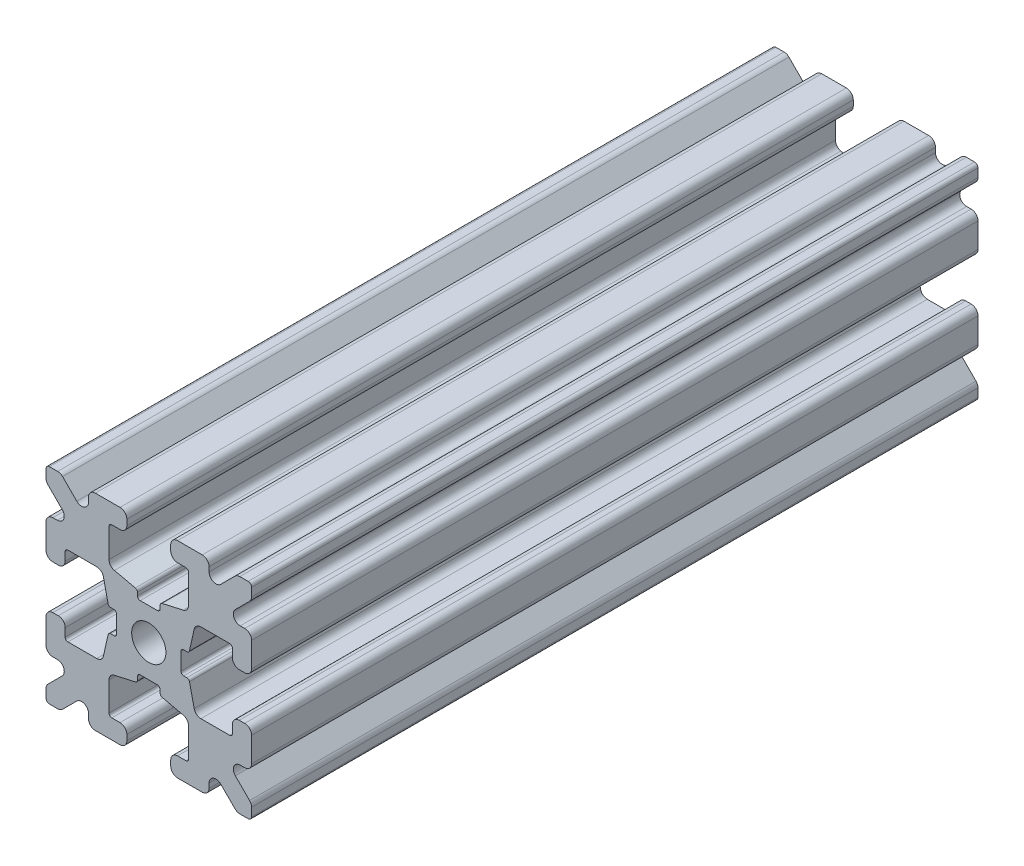
SolidWorks part; units mm, degrees
ref_plane "Front Plane" through (0, 0, 0) normal (0, 0, 1) x (1, 0, 0)
ref_plane "Top Plane" through (0, 0, 0) normal (0, 1, 0) x (1, 0, 0)
ref_plane "Right Plane" through (0, 0, 0) normal (1, 0, 0) x (0, 0, -1)
sketch "Sketch1" plane through (0, 0, 0) normal (0, 0, 1) x (1, 0, 0)
  line L1 (-7.5, -7.5) -> (7.5, -7.5)
  line L2 (-7.5, -7.5) -> (-7.5, 7.5)
  line L3 (-7.5, 7.5) -> (7.5, 7.5)
  line L4 (7.5, -7.5) -> (7.5, 7.5)
  line L5 (-7.5, -7.5) -> (7.5, 7.5) construction
  line L6 (-7.5, 7.5) -> (7.5, -7.5) construction
  circle A0 centre (0, 0) radius 1.25
  point P0 (0, 0)
  dimension "D2" = 2.5
  dimension "D1" = 15
extrude "Boss-Extrude1" add sketch "Sketch1" along normal mid plane 53
fillet "Fillet1" radius 0.25 4 edges at (7.5, -7.5, 0) (-7.5, -7.5, 0) (7.5, 7.5, 0) (-7.5, 7.5, 0)
sketch "Sketch2" plane through (0, 0, 26.5) normal (0, 0, 1) x (1, 0, 0)
  line L0 (-7.5, 7.25) -> (-7.5, -7.25) construction
  line L1 (-7.5, 1.6) -> (-6.1, 1.6)
  line L2 (-7.5, 1.6) -> (-7.5, -1.6)
  line L3 (-7.5, -1.6) -> (-6.1, -1.6)
  line L4 (-6.1, 1.6) -> (-6.1, 2.9)
  line L5 (0, 0) -> (-12.1036, 0) construction
  line L6 (-6.1, -2.9) -> (-3.4, -2.9)
  line L7 (0, 0) -> (-7.25, 7.25) construction
  line L8 (-6.1, 2.9) -> (-3.4, 2.9)
  line L9 (-3.4, -2.9) -> (-3.4, 2.9)
  line L10 (55, 0) -> (-55, 0) construction
  line L11 (-6.1, -2.9) -> (-6.1, -1.6)
  line L12 (2.9, 6.1) -> (1.6, 6.1)
  line L13 (2.9, 3.4) -> (-2.9, 3.4)
  line L14 (-2.9, 6.1) -> (-2.9, 3.4)
  line L15 (2.9, 6.1) -> (2.9, 3.4)
  line L16 (-1.6, 6.1) -> (-2.9, 6.1)
  line L17 (1.6, 7.5) -> (1.6, 6.1)
  line L18 (-1.6, 7.5) -> (1.6, 7.5)
  line L19 (-1.6, 7.5) -> (-1.6, 6.1)
  line L20 (-1.6, -7.5) -> (-1.6, -6.1)
  line L21 (-1.6, -7.5) -> (1.6, -7.5)
  line L22 (1.6, -7.5) -> (1.6, -6.1)
  line L23 (-1.6, -6.1) -> (-2.9, -6.1)
  line L24 (2.9, -6.1) -> (2.9, -3.4)
  line L25 (-2.9, -6.1) -> (-2.9, -3.4)
  line L26 (2.9, -3.4) -> (-2.9, -3.4)
  line L27 (2.9, -6.1) -> (1.6, -6.1)
  line L28 (6.1, -2.9) -> (6.1, -1.6)
  line L29 (3.4, -2.9) -> (3.4, 2.9)
  line L30 (6.1, 2.9) -> (3.4, 2.9)
  line L31 (6.1, -2.9) -> (3.4, -2.9)
  line L32 (6.1, 1.6) -> (6.1, 2.9)
  line L33 (7.5, -1.6) -> (6.1, -1.6)
  line L34 (7.5, 1.6) -> (7.5, -1.6)
  line L35 (7.5, 1.6) -> (6.1, 1.6)
  dimension "D1" = 3.2
  dimension "D2" = 5.8
  dimension "D3" = 1.4
  dimension "D4" = 2.7
extrude "Cut-Extrude1" cut sketch "Sketch2" against normal through all
sketch "Sketch4" plane through (0, 0, 26.5) normal (0, 0, 1) x (1, 0, 0)
  line L0 (-3.4, 2.9) -> (-2.75, 0)
  line L1 (55, 0) -> (-55, 0) construction
  line L2 (-2.75, 0) -> (-3.4, -2.9)
  line L3 (-3.4, -2.9) -> (-3.4, 2.9) construction
  line L4 (-3.4, 2.9) -> (-3.4, -2.9)
  line L5 (-2.9, 3.4) -> (0, 2.75)
  line L6 (0, 2.75) -> (2.9, 3.4)
  line L7 (2.9, 3.4) -> (-2.9, 3.4)
  line L8 (3.4, 2.9) -> (2.75, 0)
  line L9 (2.75, 0) -> (3.4, -2.9)
  line L10 (3.4, -2.9) -> (3.4, 2.9)
  line L11 (-2.9, -3.4) -> (0, -2.75)
  line L12 (0, -2.75) -> (2.9, -3.4)
  line L13 (2.9, -3.4) -> (-2.9, -3.4)
  circle A2 centre (0, 0) radius 2.75
  circle A3 centre (0, 0) radius 2.75 construction
  dimension "D1" = 1.5
extrude "Cut-Extrude3" cut sketch "Sketch4" against normal through all
fillet "Fillet3" radius 0.5 16 edges at (-6.1, -1.6, 0) (-7.5, -1.6, 0) (-6.1, 1.6, 0) (-7.5, 1.6, 0) (-1.6, -7.5, 0) (-1.6, -6.1, 0) (1.6, -7.5, 0) (1.6, -6.1, 0) (6.1, -1.6, 0) (7.5, -1.6, 0) (7.5, 1.6, 0) (6.1, 1.6, 0) (1.6, 7.5, 0) (1.6, 6.1, 0) (-1.6, 7.5, 0) (-1.6, 6.1, 0)
fillet "Fillet4" radius 0.5 8 edges at (-3.4, 2.9, 0) (-3.4, -2.9, 0) (2.9, -3.4, 0) (-2.9, -3.4, 0) (3.4, -2.9, 0) (3.4, 2.9, 0) (-2.9, 3.4, 0) (2.9, 3.4, 0)
fillet "Fillet5" radius 3 4 edges at (0, -2.75, 0) (2.75, 0, 0) (-2.75, 0, 0) (0, 2.75, 0)
fillet "Fillet6" radius 0.2 8 edges at (-2.9, -6.1, 0) (2.9, -6.1, 0) (6.1, -2.9, 0) (6.1, 2.9, 0) (2.9, 6.1, 0) (-2.9, 6.1, 0) (-6.1, -2.9, 0) (-6.1, 2.9, 0)
sketch "Sketch5" plane through (0, 0, 26.5) normal (0, 0, 1) x (1, 0, 0)
  line L0 (0, 0) -> (-7.25, 7.25) construction
  line L1 (-7.5, 6.4393) -> (-5.4607, 4.4)
  line L2 (-6.4393, 7.5) -> (-4.4, 5.4607)
  line L3 (-7.5, 4.4) -> (-5.4607, 4.4)
  line L4 (-3.8003, 2.9) -> (-5.9, 2.9) construction
  line L5 (0, 0) -> (-12.1819, 0) construction
  line L6 (-4.4, 7.5) -> (-4.4, 5.4607)
  line L7 (-2.9, 5.9) -> (-2.9, 3.8003) construction
  line L8 (-7.5, 6.4393) -> (-7.5, 4.4)
  line L9 (-7.5, 7.25) -> (-7.5, 2.1) construction
  line L10 (2.1, -7.5) -> (7.25, -7.5) construction
  line L11 (7.5, -7.25) -> (7.5, -2.1) construction
  line L12 (7.25, 7.5) -> (2.1, 7.5) construction
  line L13 (-2.1, 7.5) -> (-7.25, 7.5) construction
  line L14 (-4.4, 7.5) -> (-6.4393, 7.5)
  line L16 (55, 0) -> (-55, 0) construction
  line L17 (0, 0) -> (0, 10.993) construction
  line L18 (0, -54.6431) -> (0, 54.6431) construction
  line L20 (4.4, 7.5) -> (6.4393, 7.5)
  line L22 (7.5, 6.4393) -> (7.5, 4.4)
  line L23 (4.4, 7.5) -> (4.4, 5.4607)
  line L24 (7.5, 4.4) -> (5.4607, 4.4)
  line L25 (6.4393, 7.5) -> (4.4, 5.4607)
  line L26 (7.5, 6.4393) -> (5.4607, 4.4)
  line L27 (7.5, -6.4393) -> (5.4607, -4.4)
  line L28 (6.4393, -7.5) -> (4.4, -5.4607)
  line L29 (7.5, -4.4) -> (5.4607, -4.4)
  line L30 (4.4, -7.5) -> (4.4, -5.4607)
  line L31 (7.5, -6.4393) -> (7.5, -4.4)
  line L33 (4.4, -7.5) -> (6.4393, -7.5)
  line L36 (-4.4, -7.5) -> (-6.4393, -7.5)
  line L38 (-7.5, -6.4393) -> (-7.5, -4.4)
  line L39 (-4.4, -7.5) -> (-4.4, -5.4607)
  line L40 (-7.5, -4.4) -> (-5.4607, -4.4)
  line L41 (-6.4393, -7.5) -> (-4.4, -5.4607)
  line L42 (-7.5, -6.4393) -> (-5.4607, -4.4)
  dimension "D1" = 1.5
  dimension "D2" = 1.5
  dimension "D3" = 1.5
extrude "Cut-Extrude4" cut sketch "Sketch5" against normal through all
fillet "Fillet8" radius 0.5 24 edges at (-5.4607, 4.4, 0) (-7.5, 4.4, 0) (-5.4607, -4.4, 0) (-7.5, -4.4, 0) (-4.4, -7.5, 0) (-4.4, -5.4607, 0) (4.4, -7.5, 0) (4.4, -5.4607, 0) (5.4607, -4.4, 0) (7.5, -4.4, 0) (7.5, 4.4, 0) (5.4607, 4.4, 0) (4.4, 5.4607, 0) (4.4, 7.5, 0) (-4.4, 5.4607, 0) (-4.4, 7.5, 0) (-6.4393, 7.5, 0) (-7.5, 6.4393, 0) (6.4393, 7.5, 0) (7.5, 6.4393, 0) (6.4393, -7.5, 0) (7.5, -6.4393, 0) (-6.4393, -7.5, 0) (-7.5, -6.4393, 0)
sketch "Sketch6" plane through (0, 0, 26.5) normal (0, 0, 1) x (1, 0, 0)
  line L0 (0, 0) -> (0, 11.013) construction
  line L1 (0.6561, 2.8971) -> (2.1235, 2.8971) construction
  line L2 (0, -54.6431) -> (0, 54.6431) construction
  line L3 (0, 0) -> (7.25, 7.25) construction
  line L4 (7.5, 0.8255) -> (7.5, -0.8255)
  line L5 (2.3471, 0.8255) -> (7.5, 0.8255)
  line L6 (0, 0) -> (12.4016, 0) construction
  line L7 (0.8255, -7.5) -> (-0.8255, -7.5)
  line L8 (2.3471, -0.8255) -> (2.3471, 0.8255)
  line L9 (0.8255, -2.3471) -> (0.8255, -7.5)
  line L10 (7.5, -0.8255) -> (2.3471, -0.8255)
  line L11 (-7.5, -0.8255) -> (-2.3471, -0.8255)
  line L12 (-2.3471, -0.8255) -> (-2.3471, 0.8255)
  line L13 (-0.8255, -2.3471) -> (0.8255, -2.3471)
  line L14 (-0.8255, 7.5) -> (-0.8255, 2.3471)
  line L15 (-0.8255, 2.3471) -> (0.8255, 2.3471)
  line L16 (-0.8255, -7.5) -> (-0.8255, -2.3471)
  line L17 (0.8255, 2.3471) -> (0.8255, 7.5)
  line L18 (0.8255, 7.5) -> (-0.8255, 7.5)
  line L19 (3.9, 7.5) -> (2.1, 7.5) construction
  line L20 (-2.3471, 0.8255) -> (-7.5, 0.8255)
  line L21 (-7.5, 0.8255) -> (-7.5, -0.8255)
  point P5 (0, -2.5973)
  point P7 (0, 2.5973)
  dimension "D3" = 0.55
  dimension "D1" = 1.651
extrude "Cut-Extrude5" cut sketch "Sketch6" against normal through all
fillet "Fillet10" radius 0.2 16 edges at (-2.935, 0.8255, 0) (-2.935, -0.8255, 0) (2.935, -0.8255, 0) (2.935, 0.8255, 0) (0.8255, 2.935, 0) (-0.8255, 2.935, 0) (-2.3471, 0.8255, 0) (-2.3471, -0.8255, 0) (0.8255, 2.3471, 0) (-0.8255, 2.3471, 0) (2.3471, 0.8255, 0) (2.3471, -0.8255, 0) (0.8255, -2.935, 0) (0.8255, -2.3471, 0) (-0.8255, -2.3471, 0) (-0.8255, -2.935, 0)
